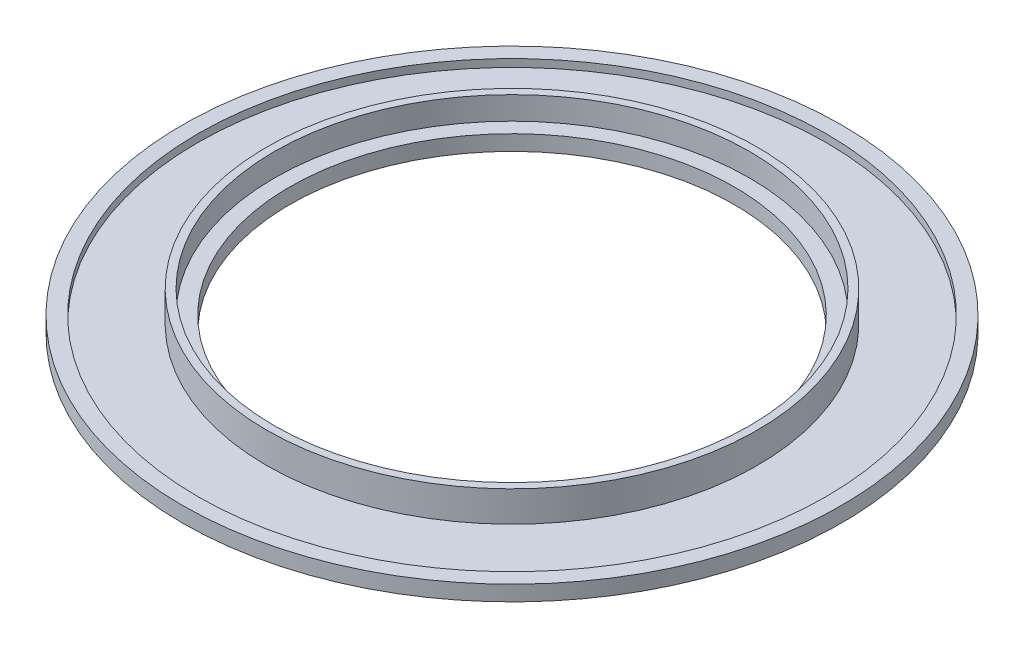
SolidWorks part; units mm, degrees
ref_plane "Front Plane" through (0, 0, 0) normal (0, 0, 1) x (1, 0, 0)
ref_plane "Top Plane" through (0, 0, 0) normal (0, 1, 0) x (1, 0, 0)
ref_plane "Right Plane" through (0, 0, 0) normal (1, 0, 0) x (0, 0, -1)
sketch "Sketch1" plane through (0, 0, 0) normal (0, 1, 0) x (1, 0, 0)
  circle A0 centre (0, 0) radius 43
  dimension "D1" = 86
extrude "Boss-Extrude1" add sketch "Sketch1" along normal blind 2
sketch "Sketch2" plane through (0, 2, 0) normal (0, 1, 0) x (1, 0, 0)
  circle A0 centre (0, 0) radius 41
  dimension "D1" = 82
extrude "Boss-Extrude2" add sketch "Sketch2" along normal blind 3
sketch "Sketch3" plane through (0, 5, 0) normal (0, 1, 0) x (1, 0, 0)
  circle A0 centre (0, 0) radius 30
  dimension "D1" = 60
extrude "Cut-Extrude1" cut sketch "Sketch3" against normal blind 2
sketch "Sketch4" plane through (0, 3, 0) normal (0, 1, 0) x (1, 0, 0)
  circle A0 centre (0, 0) radius 28
  dimension "D1" = 56
extrude "Cut-Extrude2" cut sketch "Sketch4" against normal through all
sketch "Sketch5" plane through (0, 5, 0) normal (0, 1, 0) x (1, 0, 0)
  circle A0 centre (0, 0) radius 41
  dimension "D1" = 82
extrude "Cut-Extrude3" cut sketch "Sketch5" against normal blind 4
sketch "Sketch6" plane through (0, 1, 0) normal (0, 1, 0) x (1, 0, 0)
  circle A0 centre (0, 0) radius 32
  dimension "D1" = 64
extrude "Boss-Extrude4" add sketch "Sketch6" along normal blind 4
sketch "Sketch7" plane through (0, 5, 0) normal (0, 1, 0) x (1, 0, 0)
  circle A0 centre (0, 0) radius 31
  dimension "D1" = 62
extrude "Cut-Extrude4" cut sketch "Sketch7" against normal blind 3
sketch "Sketch8" plane through (0, 2, 0) normal (0, 1, 0) x (1, 0, 0)
  circle A0 centre (0, 0) radius 29
  dimension "D1" = 58
extrude "Cut-Extrude5" cut sketch "Sketch8" against normal through all
